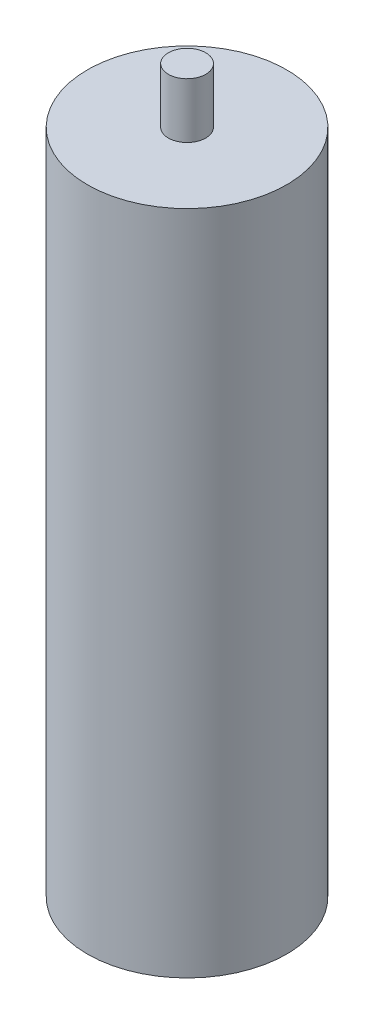
SolidWorks part; units mm, degrees
ref_plane "Front Plane" through (0, 0, 0) normal (0, 0, 1) x (1, 0, 0)
ref_plane "Top Plane" through (0, 0, 0) normal (0, 1, 0) x (1, 0, 0)
ref_plane "Right Plane" through (0, 0, 0) normal (1, 0, 0) x (0, 0, -1)
sketch "Sketch1" plane through (0, 0, 0) normal (0, 1, 0) x (1, 0, 0)
  circle A0 centre (0, 0) radius 6.096
extrude "Boss-Extrude8" add sketch "Sketch1" along normal blind 40.767
sketch "Sketch7" plane through (0, 0, 0) normal (0, -1, 0) x (1, 0, 0)
  circle A0 centre (0, 0) radius 1.143
extrude "Boss-Extrude10" add sketch "Sketch7" along normal blind 3.3782 contours A0
sketch "Sketch8" plane through (0, 40.767, 0) normal (0, 1, 0) x (1, 0, 0)
  circle A0 centre (0, 0) radius 1.143
extrude "Boss-Extrude12" add sketch "Sketch8" along normal blind 3.3782 contours A0
